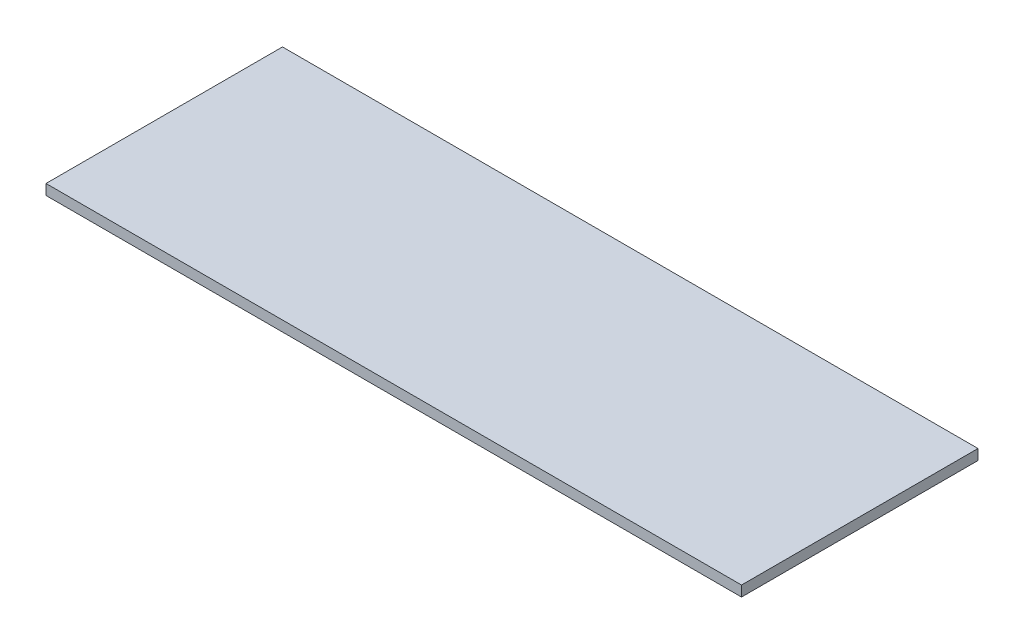
SolidWorks part; units mm, degrees
ref_plane "Front Plane" through (0, 0, 0) normal (0, 0, 1) x (1, 0, 0)
ref_plane "Top Plane" through (0, 0, 0) normal (0, 1, 0) x (1, 0, 0)
ref_plane "Right Plane" through (0, 0, 0) normal (1, 0, 0) x (0, 0, -1)
sketch "Sketch1" plane through (0, 0, 0) normal (0, 1, 0) x (1, 0, 0)
  line L1 (-123.0837, 60.9824) -> (130.9163, 60.9824)
  line L2 (-123.0837, 60.9824) -> (-123.0837, -25.3776)
  line L3 (-123.0837, -25.3776) -> (130.9163, -25.3776)
  line L4 (130.9163, 60.9824) -> (130.9163, -25.3776)
  dimension "D1" = 254
  dimension "D2" = 86.36
extrude "Boss-Extrude1" add sketch "Sketch1" along normal blind 3.81 contours L1 L4 L3 L2
